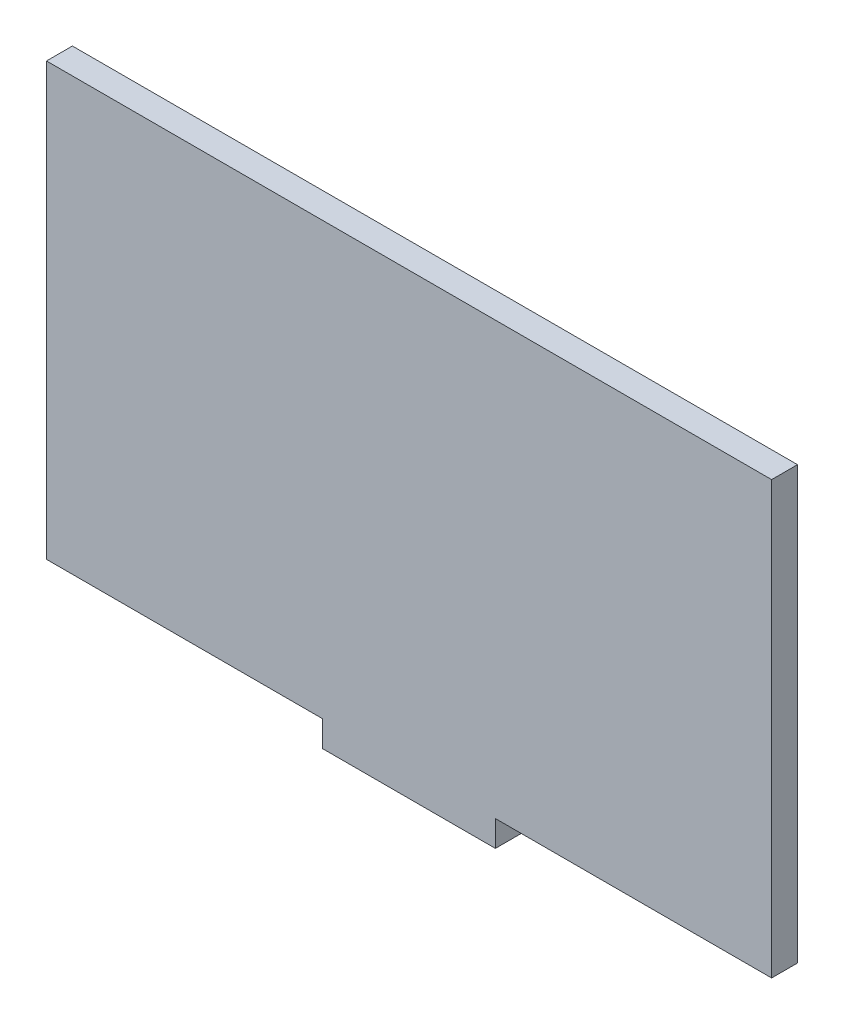
SolidWorks part; units mm, degrees
ref_plane "Alzado" through (0, 0, 0) normal (0, 0, 1) x (1, 0, 0)
ref_plane "Planta" through (0, 0, 0) normal (0, 1, 0) x (1, 0, 0)
ref_plane "Vista lateral" through (0, 0, 0) normal (1, 0, 0) x (0, 0, -1)
sketch "Croquis1" plane through (0, 0, 0) normal (0, 0, 1) x (1, 0, 0)
  line L1 (-42, 25) -> (42, 25)
  line L2 (-42, 25) -> (-42, -25)
  line L3 (-42, -25) -> (42, -25)
  line L4 (42, 25) -> (42, -25)
  line L5 (-42, 25) -> (42, -25) construction
  line L6 (-42, -25) -> (42, 25) construction
  point P0 (0, 0)
  dimension "D1" = 84
  dimension "D2" = 50
extrude "Saliente-Extruir1" add sketch "Croquis1" along normal blind 3
sketch "Croquis2" plane through (0, 0, 3) normal (0, 0, 1) x (1, 0, 0)
  line L0 (0, 0) -> (0, -14.1471) construction
  line L1 (-42, -25) -> (42, -25) construction
  line L2 (-10, -25) -> (10, -25)
  line L3 (-10, -25) -> (-10, -28)
  line L4 (-10, -28) -> (10, -28)
  line L5 (10, -25) -> (10, -28)
  dimension "D1" = 10
  dimension "D2" = 20
  dimension "D3" = 3
extrude "Saliente-Extruir2" add sketch "Croquis2" against normal blind 3
